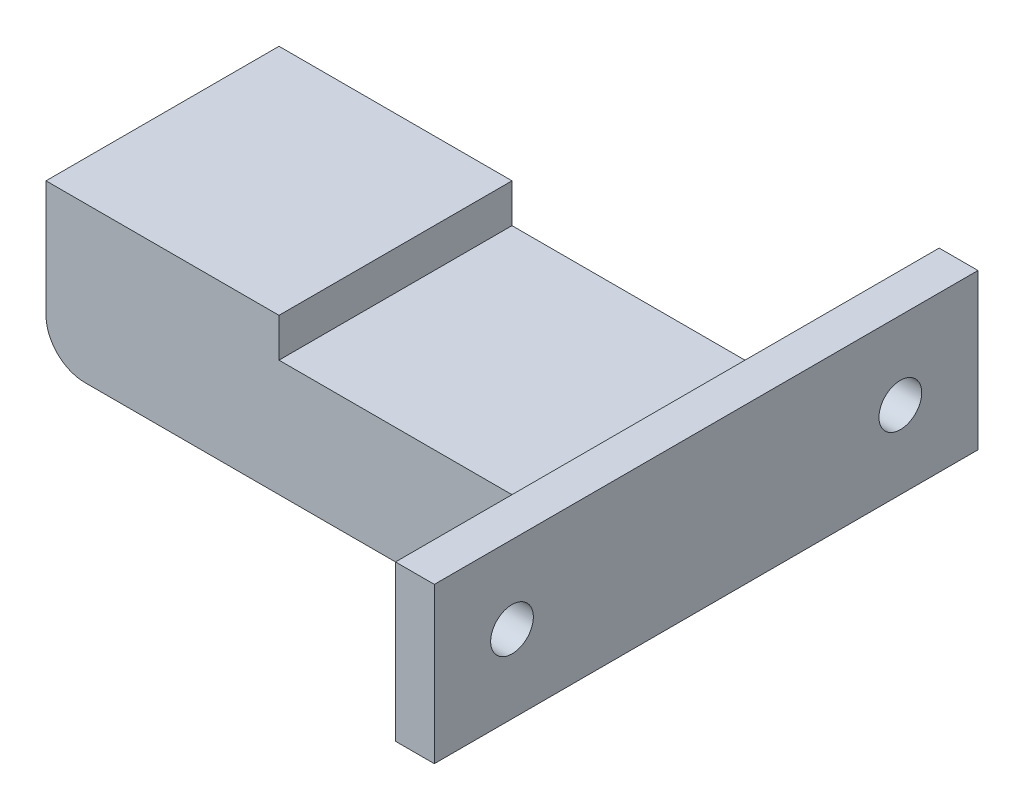
SolidWorks part; units mm, degrees
ref_plane "Front Plane" through (0, 0, 0) normal (0, 0, 1) x (1, 0, 0)
ref_plane "Top Plane" through (0, 0, 0) normal (0, 1, 0) x (1, 0, 0)
ref_plane "Right Plane" through (0, 0, 0) normal (1, 0, 0) x (0, 0, -1)
sketch "Sketch1" plane through (0, 0, 0) normal (0, 1, 0) x (1, 0, 0)
  line L1 (0, 0) -> (70, 0)
  line L2 (0, 0) -> (0, 30)
  line L3 (0, 30) -> (70, 30)
  line L4 (70, 0) -> (70, 30)
  dimension "D1" = 70
  dimension "D2" = 30
extrude "Boss-Extrude1" add sketch "Sketch1" along normal blind 20
sketch "Sketch8" plane through (70, 0, 0) normal (1, 0, 0) x (0, 0, -1)
  line L0 (0, 20) -> (-20, 0) construction
  line L1 (0, 20) -> (-20, 20)
  line L2 (0, 20) -> (0, 0)
  line L3 (0, 0) -> (-20, 0)
  line L4 (-20, 20) -> (-20, 0)
  circle A0 centre (-10, 10) radius 2.75
  dimension "D2" = 5.5
  dimension "D1" = 20
extrude "Boss-Extrude5" add sketch "Sketch8" against normal blind 5
ref_plane "Plane1" through (0, 0, -15) normal (0, 0, 1) x (1, 0, 0)
mirror "Mirror1" about plane through (0, 0, -15) normal (0, 0, 1) of "Boss-Extrude5"
fillet "Fillet3" radius 5 3 edges at (65, 10, 0) (65, 10, -30) (0, 0, -15)
sketch "Sketch9" plane through (0, 20, 0) normal (0, 1, 0) x (1, 0, 0)
  line L0 (0, 30) -> (0, 0) construction
  line L1 (65, 35) -> (30, 35)
  line L2 (65, 35) -> (65, -5)
  line L3 (65, -5) -> (30, -5)
  line L4 (30, 35) -> (30, -5)
  point P5 (65, -5)
  dimension "D1" = 30
extrude "Cut-Extrude5" cut sketch "Sketch9" against normal blind 5
